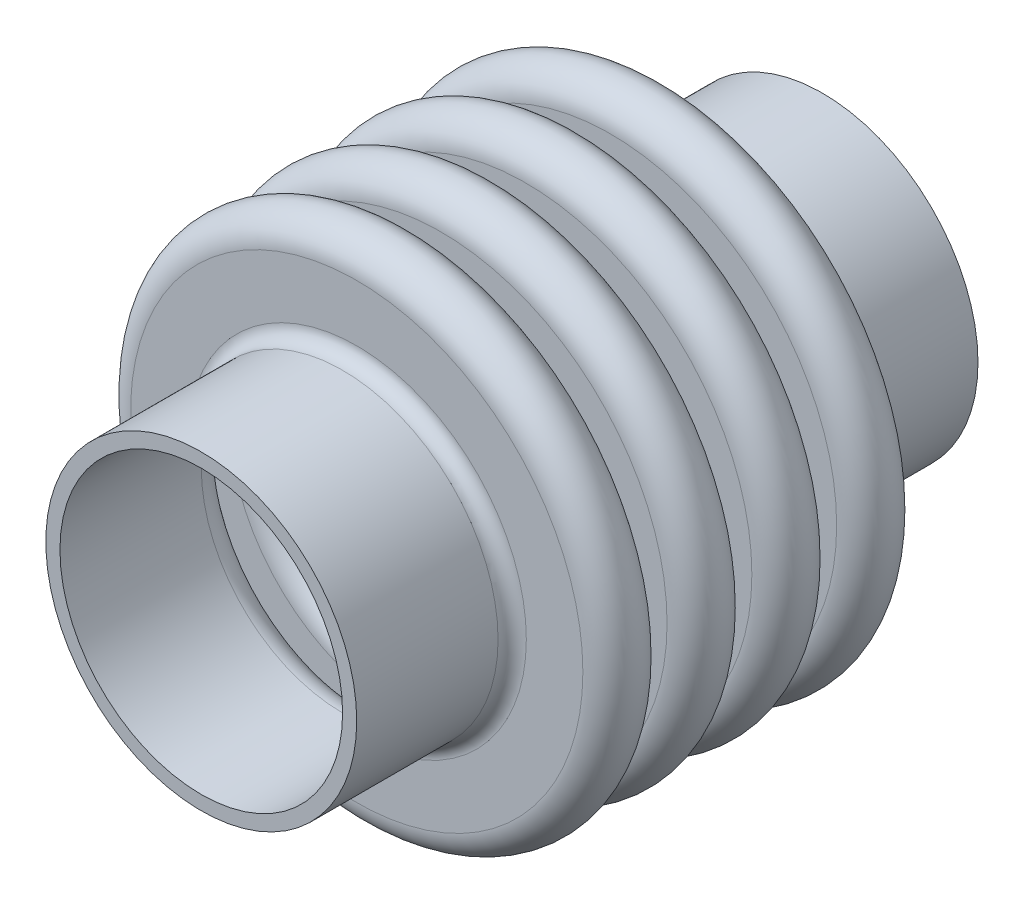
SolidWorks part; units mm, degrees
material "AISI Type 316L stainless steel"
ref_plane "Front Plane" through (0, 0, 0) normal (0, 0, 1) x (1, 0, 0)
ref_plane "Top Plane" through (0, 0, 0) normal (0, 1, 0) x (1, 0, 0)
ref_plane "Right Plane" through (0, 0, 0) normal (1, 0, 0) x (0, 0, -1)
sketch "Sketch1" plane through (0, 0, 0) normal (1, 0, 0) x (0, 0, -1)
  line L0 (-39.0149, 0) -> (68.4944, 0) construction
  line L1 (-43.18, 27.94) -> (-17.78, 27.94)
  line L2 (-43.18, 25.4) -> (-17.78, 25.4)
  line L3 (-15.24, 30.48) -> (-15.24, 40.64)
  line L4 (-12.7, 30.48) -> (-12.7, 40.64)
  line L5 (-7.62, 40.64) -> (-7.62, 30.48)
  line L6 (-5.08, 40.64) -> (-5.08, 30.48)
  line L7 (-0.109, 30.48) -> (-0.109, 40.64)
  line L8 (2.431, 30.48) -> (2.431, 40.64)
  line L9 (7.511, 40.64) -> (7.511, 30.48)
  line L10 (10.051, 40.64) -> (10.051, 30.48)
  line L11 (15.131, 30.48) -> (15.131, 40.64)
  line L12 (17.671, 30.48) -> (17.671, 40.64)
  line L13 (22.751, 40.64) -> (22.751, 30.48)
  line L14 (25.291, 40.64) -> (25.291, 30.48)
  line L15 (30.371, 30.48) -> (30.371, 40.64)
  line L16 (32.911, 30.48) -> (32.911, 40.64)
  line L17 (37.991, 40.64) -> (37.991, 30.48)
  line L18 (40.531, 40.64) -> (40.531, 30.48)
  line L19 (43.071, 27.94) -> (68.471, 27.94)
  line L20 (43.071, 25.4) -> (68.471, 25.4)
  line L21 (68.471, 27.94) -> (68.471, 25.4)
  line L22 (-43.18, 27.94) -> (-43.18, 25.4)
  arc A0 (-17.78, 27.94) -> (-15.24, 30.48) centre (-17.78, 30.48) ccw
  arc A1 (-17.78, 25.4) -> (-12.7, 30.48) centre (-17.78, 30.48) ccw
  arc A2 (-12.7, 40.64) -> (-7.62, 40.64) centre (-10.16, 40.64) cw
  arc A3 (-15.24, 40.64) -> (-5.08, 40.64) centre (-10.16, 40.64) cw
  arc A4 (-7.62, 30.48) -> (2.431, 30.48) centre (-2.5945, 30.48) ccw
  arc A5 (-5.08, 30.48) -> (-0.109, 30.48) centre (-2.5945, 30.48) ccw
  arc A6 (2.431, 40.64) -> (7.511, 40.64) centre (4.971, 40.64) cw
  arc A7 (-0.109, 40.64) -> (10.051, 40.64) centre (4.971, 40.64) cw
  arc A8 (10.051, 30.48) -> (15.131, 30.48) centre (12.591, 30.48) ccw
  arc A9 (7.511, 30.48) -> (17.671, 30.48) centre (12.591, 30.48) ccw
  arc A10 (17.671, 40.64) -> (22.751, 40.64) centre (20.211, 40.64) cw
  arc A11 (15.131, 40.64) -> (25.291, 40.64) centre (20.211, 40.64) cw
  arc A12 (25.291, 30.48) -> (30.371, 30.48) centre (27.831, 30.48) ccw
  arc A13 (22.751, 30.48) -> (32.911, 30.48) centre (27.831, 30.48) ccw
  arc A14 (32.911, 40.64) -> (37.991, 40.64) centre (35.451, 40.64) cw
  arc A15 (30.371, 40.64) -> (40.531, 40.64) centre (35.451, 40.64) cw
  arc A16 (40.531, 30.48) -> (43.071, 27.94) centre (43.071, 30.48) ccw
  arc A17 (37.991, 30.48) -> (43.071, 25.4) centre (43.071, 30.48) ccw
  dimension "D3" = 2.54
  dimension "D4" = 2.54
  dimension "D5" = 2.4855
  dimension "D6" = 10.16
  dimension "D9" = 2.54
  dimension "D10" = 2.54
  dimension "D11" = 2.54
  dimension "D12" = 2.54
  dimension "D13" = 2.54
  dimension "D14" = 2.54
  dimension "D1" = 25.4
  dimension "D2" = 27.94
  dimension "D7" = 17.78
  dimension "D8" = 25.4
  dimension "D15" = 25.4
revolve "Revolve1" add sketch "Sketch1" angle 360 about L0
